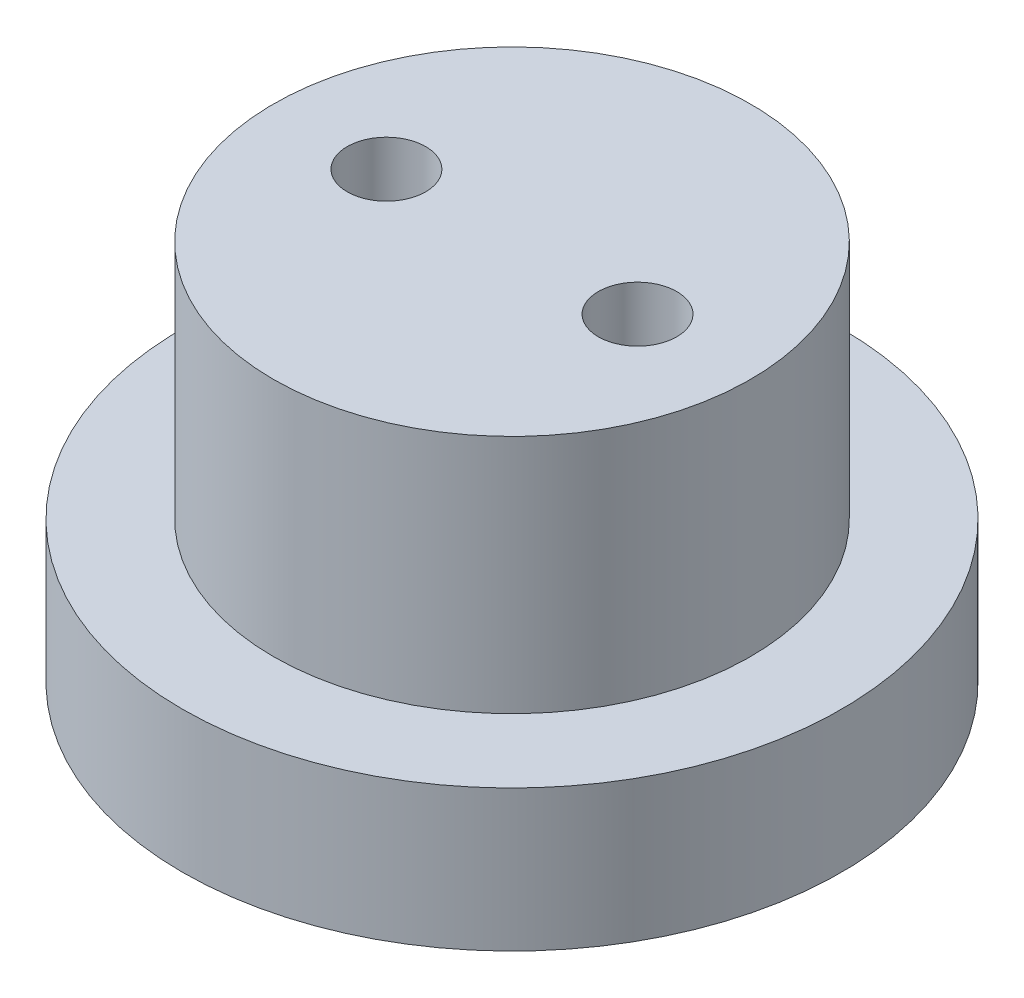
SolidWorks part; units mm, degrees
material "PVC 0.007 Plasticized"
ref_plane "Front Plane" through (0, 0, 0) normal (0, 0, 1) x (1, 0, 0)
ref_plane "Top Plane" through (0, 0, 0) normal (0, 1, 0) x (1, 0, 0)
ref_plane "Right Plane" through (0, 0, 0) normal (1, 0, 0) x (0, 0, -1)
sketch "Sketch2" plane through (0, 0, 0) normal (0, 1, 0) x (1, 0, 0)
  circle A0 centre (0, 0) radius 7.6
  circle A1 centre (0, 0) radius 4 construction
  circle A2 centre (4, 0) radius 1.25
  circle A3 centre (-4, 0) radius 1.25
  dimension "D1" = 15.2
  dimension "D3" = 8
  dimension "D4" = 2.5
  dimension "D2" = 0
extrude "Boss-Extrude2" add sketch "Sketch2" along normal blind 10.15 separate body
sketch "Sketch3" plane through (0, 0, 0) normal (0, 1, 0) x (1, 0, 0)
  circle A0 centre (0, 0) radius 10.5
  circle A1 centre (-4, 0) radius 1.25 construction
  circle A2 centre (-4, 0) radius 1.25
  circle A3 centre (4, 0) radius 1.25 construction
  circle A4 centre (4, 0) radius 1.25
  dimension "D1" = 21
extrude "Boss-Extrude3" add sketch "Sketch3" along normal blind 2.5
sketch "Sketch4" plane through (0, 0, 0) normal (0, -1, 0) x (1, 0, 0)
  circle A0 centre (4, 0) radius 2.675
  circle A1 centre (-4, 0) radius 2.675
  dimension "D1" = 5.35
extrude "Cut-Extrude1" cut sketch "Sketch4" against normal offset from surface (2.15 mm away) 8 up to face at (4, 10.15, 1.25)
sketch "Sketch5" plane through (0, 0, 0) normal (0, -1, 0) x (1, 0, 0)
  circle A1 centre (-4, 0) radius 2.675
  circle A2 centre (-4, 0) radius 2.675
  circle A3 centre (4, 0) radius 2.675
  circle A4 centre (4, 0) radius 2.675
  circle A5 centre (0, 0) radius 10.5
  circle A6 centre (0, 0) radius 10.5
  dimension "D1" = 0
  dimension "D2" = 0
  dimension "D3" = 0
extrude "Boss-Extrude4" add sketch "Sketch5" along normal blind 2
